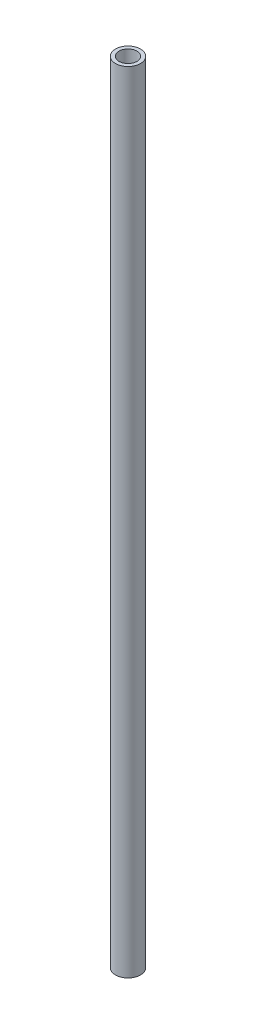
SolidWorks part; units mm, degrees
ref_plane "Front Plane" through (0, 0, 0) normal (0, 0, 1) x (1, 0, 0)
ref_plane "Top Plane" through (0, 0, 0) normal (0, 1, 0) x (1, 0, 0)
ref_plane "Right Plane" through (0, 0, 0) normal (1, 0, 0) x (0, 0, -1)
sketch "Sketch1" plane through (0, 0, 0) normal (0, 1, 0) x (1, 0, 0)
  circle A0 centre (0, 0) radius 2.5
  circle A1 centre (0, 0) radius 3.5
  dimension "D1" = 5
  dimension "D2" = 7
extrude "Boss-Extrude1" add sketch "Sketch1" along normal mid plane 220
